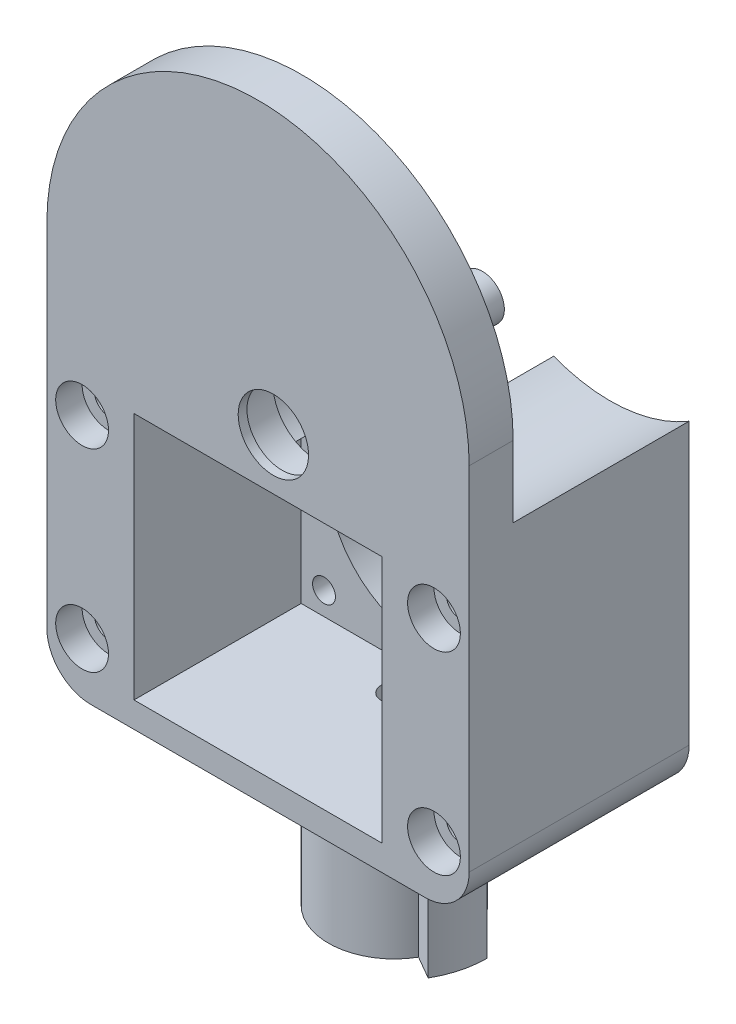
SolidWorks part; units mm, degrees
ref_plane "前视基准面" through (0, 0, 0) normal (0, 0, 1) x (1, 0, 0)
ref_plane "上视基准面" through (0, 0, 0) normal (0, 1, 0) x (1, 0, 0)
ref_plane "右视基准面" through (0, 0, 0) normal (1, 0, 0) x (0, 0, -1)
sketch "草图1" plane through (0, 0, 0) normal (0, 0, 1) x (1, 0, 0)
  line L0 (-24, 0) -> (-24, -45)
  line L1 (-24, -45) -> (24, -45)
  line L2 (24, -45) -> (24, 0)
  arc A0 (24, 0) -> (-24, 0) centre (0, 0) ccw
  dimension "D1" = 24
  dimension "D2" = 45
extrude "凸台-拉伸1" add sketch "草图1" along normal blind 25
sketch "草图2" plane through (0, 0, 0) normal (0, 0, -1) x (-1, 0, 0)
  line L0 (-1.7431, -8.0761) -> (0, -28) construction
  line L1 (0, -28) -> (0, 0) construction
  circle A0 centre (0, -28) radius 5
  circle A1 centre (-1.7431, -8.0761) radius 15
  circle A2 centre (-15, 6.899) radius 15
  circle A3 centre (15, 6.899) radius 15
  circle A4 centre (-1.7431, -8.0761) radius 5
  dimension "D1" = 10
  dimension "D2" = 30
  dimension "D3" = 30
  dimension "D4" = 10
  dimension "D5" = 28
  dimension "D6" = 5
sketch "草图3" plane through (0, 0, 25) normal (0, 0, 1) x (1, 0, 0)
  line L1 (-14.1, -13.9) -> (14.1, -13.9)
  line L2 (-14.1, -13.9) -> (-14.1, -42.1)
  line L3 (-14.1, -42.1) -> (14.1, -42.1)
  line L4 (14.1, -13.9) -> (14.1, -42.1)
  line L5 (0, -42.1) -> (0, -13.9) construction
  line L6 (-14.1, -28) -> (14.1, -28) construction
  point P0 (0, -28)
  dimension "D1" = 28.2
  dimension "D2" = 28.2
extrude "切除-拉伸1" cut sketch "草图3" against normal offset from surface (19 mm away) 6 up to face at (0, -16.5, 0)
sketch "草图4" plane through (0, 0, 0) normal (0, 0, -1) x (-1, 0, 0)
  circle A0 centre (0, -28) radius 11.1
  dimension "D1" = 22.2
extrude "切除-拉伸2" cut sketch "草图4" against normal through all
sketch "草图8" plane through (0, 0, 0) normal (0, 0, -1) x (-1, 0, 0)
  line L0 (-15, 24.399) -> (15, 24.399)
  arc A1 (-8.6176, -9.3956) -> (5.2425, -7.6282) centre (-1.7431, -8.0761) ccw
  arc A2 (-15, 24.399) -> (-8.6176, -9.3956) centre (-15, 6.899) ccw
  arc A3 (5.2425, -7.6282) -> (15, 24.399) centre (15, 6.899) ccw
  arc A4 (-8.6176, -9.3956) -> (5.2425, -7.6282) centre (-1.7431, -8.0761) ccw
  arc A5 (5.2425, -7.6282) -> (15, 24.399) centre (15, 6.899) ccw
  arc A7 (-15, 24.399) -> (-8.6176, -9.3956) centre (-15, 6.899) ccw
  arc M5 (24, 0) -> (-24, 0) centre (0, 0) ccw
  line M6 (-24, 0) -> (-24, -45)
  line M8 (24, -45) -> (24, 0)
  dimension "D1" = 35
  dimension "D2" = 14
  dimension "D3" = 17.5
extrude "切除-拉伸3" cut sketch "草图8" against normal blind 20 contours A1 A3 A2 M8 M5 M6
sketch "草图11" plane through (0, 0, 20) normal (0, 0, -1) x (-1, 0, 0)
  circle A0 centre (-15, 6.899) radius 3
  circle A1 centre (15, 6.899) radius 3
  dimension "D1" = 6
extrude "凸台-拉伸2" add sketch "草图11" along normal blind 0.5
sketch "草图12" plane through (0, 0, 19.5) normal (0, 0, -1) x (-1, 0, 0)
  circle A0 centre (-15, 6.899) radius 2.5
  circle A1 centre (15, 6.899) radius 2.5
  dimension "D1" = 5
extrude "凸台-拉伸3" add sketch "草图12" along normal blind 5
sketch "草图13" plane through (0, 0, 20) normal (0, 0, -1) x (-1, 0, 0)
  circle A0 centre (-1.7431, -8.0761) radius 5.05
  dimension "D1" = 10.1
extrude "切除-拉伸6" cut sketch "草图13" against normal blind 4
sketch "草图14" plane through (0, 0, 24) normal (0, 0, -1) x (-1, 0, 0)
  circle A0 centre (-1.7431, -8.0761) radius 4
  dimension "D1" = 8
extrude "切除-拉伸7" cut sketch "草图14" against normal through all
sketch "草图15" plane through (0, 0, 25) normal (0, 0, 1) x (1, 0, 0)
  line L0 (0, -28) -> (-34.8084, -28) construction
  line L1 (-24, -45) -> (24, -45) construction
  line L2 (-24, 0) -> (-24, -45) construction
  line L3 (0, -28) -> (0, 0) construction
  line L4 (0, -28) -> (0, 0) construction
  circle A1 centre (-20, -39) radius 1.6
  circle A2 centre (-20, -17) radius 1.6
  circle A3 centre (20, -39) radius 1.6
  circle A4 centre (20, -17) radius 1.6
  dimension "D3" = 3.2
  dimension "D1" = 6
  dimension "D2" = 4
extrude "切除-拉伸8" cut sketch "草图15" against normal through all
sketch "草图16" plane through (0, 0, 25) normal (0, 0, 1) x (1, 0, 0)
  circle A0 centre (-20, -17) radius 3
  circle A1 centre (-20, -39) radius 3
  circle A2 centre (20, -17) radius 3
  circle A3 centre (20, -39) radius 3
  dimension "D1" = 6
extrude "切除-拉伸9" cut sketch "草图16" against normal blind 3
sketch "草图17" plane through (0, 0, 6) normal (0, 0, 1) x (1, 0, 0)
  circle A0 centre (-11.5, -16.5) radius 1.3
  circle A1 centre (11.5, -16.5) radius 1.3
  circle A2 centre (11.5, -39.5) radius 1.3
  circle A3 centre (-11.5, -39.5) radius 1.3
  point P11 (0, -28)
  dimension "D1" = 2.6
  dimension "D3" = 23
  dimension "D2" = 4
extrude "切除-拉伸10" cut sketch "草图17" against normal through all
sketch "草图18" plane through (0, 0, 0) normal (0, 0, -1) x (-1, 0, 0)
  circle A0 centre (-11.5, -16.5) radius 2.5
  circle A1 centre (11.5, -16.5) radius 2.5
  circle A2 centre (-11.5, -39.5) radius 2.5
  circle A3 centre (11.5, -39.5) radius 2.5
  dimension "D1" = 5
extrude "切除-拉伸11" cut sketch "草图18" against normal blind 2.5
fillet "圆角1" radius 5 2 edges at (-24, -45, 12.5) (24, -45, 12.5)
sketch "草图19" plane through (0, -45, 0) normal (0, -1, 0) x (1, 0, 0)
  line L0 (0, 0) -> (30, 0) construction
  circle A0 centre (0, 9.5) radius 7.5
  dimension "D2" = 15
  dimension "D1" = 9.5
extrude "凸台-拉伸4" add sketch "草图19" along normal blind 18
sketch "草图20" plane through (0, -63, 0) normal (0, -1, 0) x (1, 0, 0)
  line L0 (-1.4465, 7.4) -> (1.4465, 7.4)
  arc A0 (1.4465, 7.4) -> (-1.4465, 7.4) centre (0, 9.5) ccw
  dimension "D1" = 2.55
  dimension "D2" = 2.1
extrude "切除-拉伸12" cut sketch "草图20" against normal blind 18
sketch "草图21" plane through (0, -45, 0) normal (0, -1, 0) x (1, 0, 0)
  circle A0 centre (0, 9.5) radius 1.5
  dimension "D1" = 3
extrude "切除-拉伸13" cut sketch "草图21" against normal blind 10
sketch "草图22" plane through (0, -45, 0) normal (0, -1, 0) x (1, 0, 0)
  line L0 (0, 9.5) -> (12.3222, 9.5) construction
  line L1 (7.5, 9.5) -> (10.5, 9.5)
  line L2 (0, 9.5) -> (10.9856, 15.8426) construction
  line L3 (6.4952, 13.25) -> (9.0933, 14.75)
  circle A0 centre (0, 9.5) radius 7.5 construction
  arc A1 (10.5, 9.5) -> (9.0933, 14.75) centre (0, 9.5) ccw
  arc A2 (7.5, 9.5) -> (6.4952, 13.25) centre (0, 9.5) ccw
  dimension "D1" = 10.5
  dimension "D2" = 30
extrude "凸台-拉伸5" add sketch "草图22" along normal up to surface (18 mm away) up to face at (0, -63, 9.725)
sketch "草图23" plane through (0, 0, 7.4) normal (0, 0, 1) x (1, 0, 0)
  line L0 (0, -63) -> (0, -53) construction
  line L1 (-1.4465, -63) -> (1.4465, -63) construction
  circle A0 centre (0, -53) radius 2
  dimension "D1" = 4
  dimension "D2" = 10
extrude "切除-拉伸14" cut sketch "草图23" against normal through all
